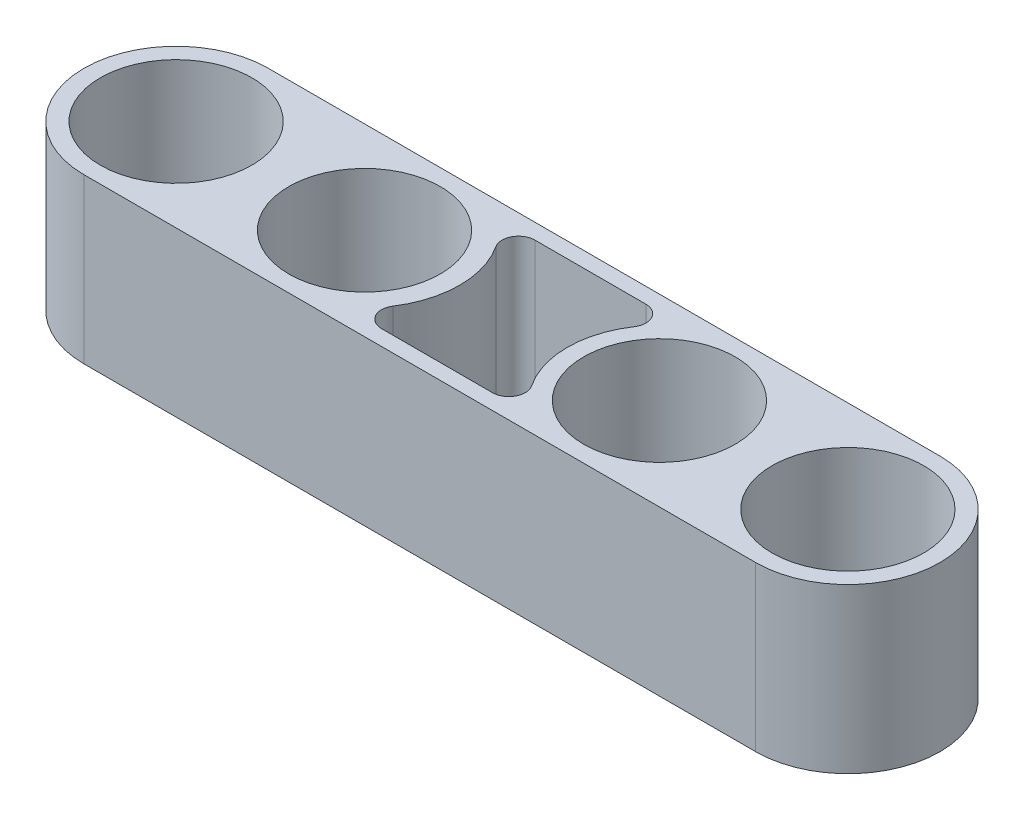
SolidWorks part; units mm, degrees
ref_plane "Front Plane" through (0, 0, 0) normal (0, 0, 1) x (1, 0, 0)
ref_plane "Top Plane" through (0, 0, 0) normal (0, 1, 0) x (1, 0, 0)
ref_plane "Right Plane" through (0, 0, 0) normal (1, 0, 0) x (0, 0, -1)
sketch "Sketch3" plane through (0, 0, 0) normal (0, 1, 0) x (1, 0, 0)
  line L0 (-41, 0) -> (-18, 0) construction
  line L1 (-18, 0) -> (18, 0) construction
  line L2 (18, 0) -> (41, 0) construction
  line L3 (-41, 0) -> (41, 0) construction
  line L4 (-41, 11.25) -> (41, 11.25)
  line L5 (-41, -11.25) -> (41, -11.25)
  line L8 (-6.5672, 9.3611) -> (6.9829, 9.3611)
  line L9 (-41, 9.25) -> (41, 9.25) construction
  line L10 (-6.5672, -9.3611) -> (6.9829, -9.3611)
  line L11 (-41, -9.25) -> (41, -9.25) construction
  circle A0 centre (-41, 0) radius 9.25
  circle A1 centre (-18, 0) radius 9.25
  circle A2 centre (18, 0) radius 9.25
  circle A3 centre (41, 0) radius 9.25
  arc A4 (-41, 11.25) -> (-41, -11.25) centre (-41, 0) ccw
  arc A5 (41, -11.25) -> (41, 11.25) centre (41, 0) ccw
  arc A7 (8.6459, 6.25) -> (8.6459, -6.25) centre (18, 0) ccw
  arc A8 (41, -9.25) -> (41, 9.25) centre (41, 0) ccw
  arc A9 (-41, 9.25) -> (-41, -9.25) centre (-41, 0) ccw
  circle A10 centre (18, 0) radius 11.25 construction
  arc A11 (-8.2437, -6.2706) -> (-8.2437, 6.2706) centre (-17.8837, 0) ccw
  arc A12 (-6.5672, -9.3611) -> (-8.2437, -6.2706) centre (-6.5672, -7.3611) cw
  arc A13 (6.9829, -9.3611) -> (8.6459, -6.25) centre (6.9829, -7.3611) ccw
  arc A14 (8.6459, 6.25) -> (6.9829, 9.3611) centre (6.9829, 7.3611) ccw
  arc A15 (-8.2437, 6.2706) -> (-6.5672, 9.3611) centre (-6.5672, 7.3611) cw
  point P8 (0, 0)
  point P9 (0, 0)
  dimension "D3" = 18.5
  dimension "D4" = 2
  dimension "D7" = 2
  dimension "D1" = 36
  dimension "D2" = 23
  dimension "D5" = 2
  dimension "D6" = 2
extrude "Boss-Extrude1" add sketch "Sketch3" along normal blind 20 contours L5 A5 L4 A4 A0 A1 A2 A3 A11 A15 L8 A14 A7 A13 L10 A12
